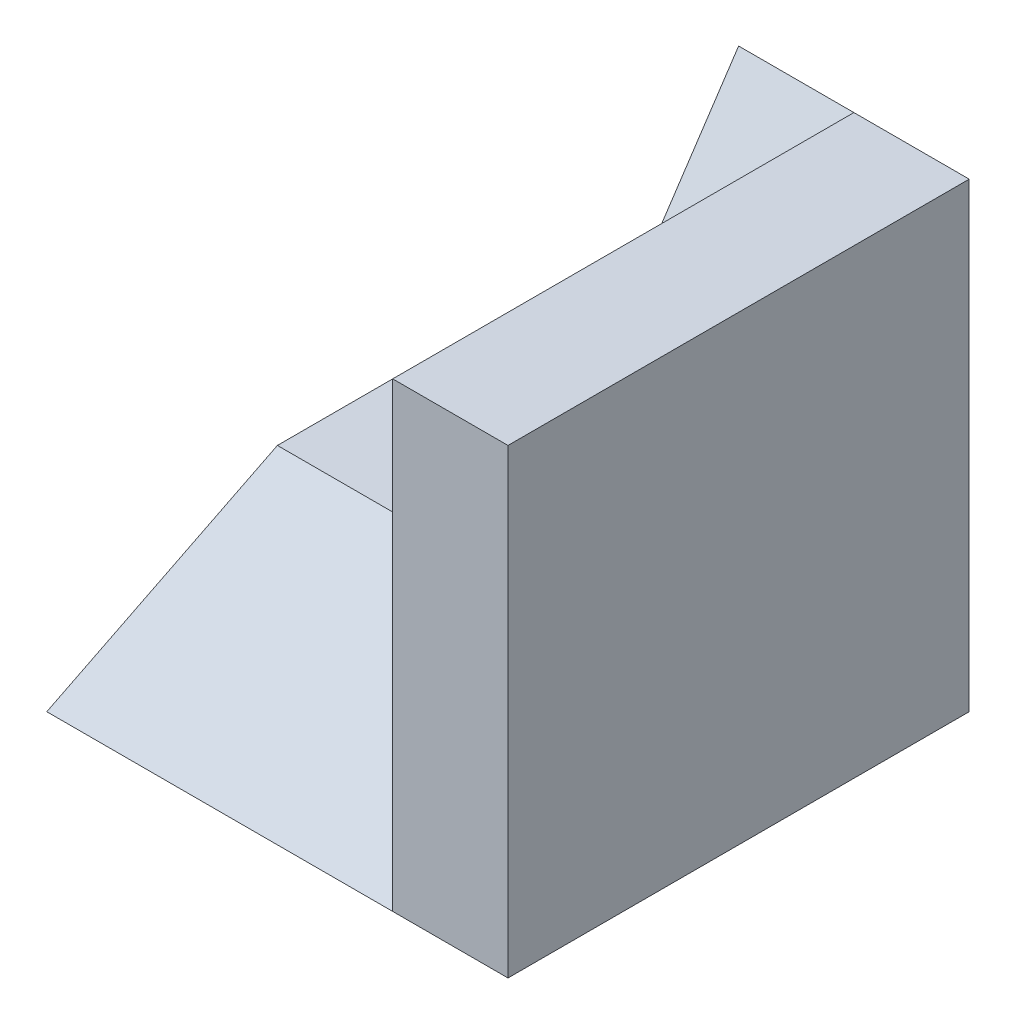
SolidWorks part; units mm, degrees
ref_plane "Front Plane" through (0, 0, 0) normal (0, 0, 1) x (1, 0, 0)
ref_plane "Top Plane" through (0, 0, 0) normal (0, 1, 0) x (1, 0, 0)
ref_plane "Right Plane" through (0, 0, 0) normal (1, 0, 0) x (0, 0, -1)
sketch "Sketch1" plane through (0, 0, 0) normal (0, 1, 0) x (1, 0, 0)
  line L1 (-2, -2) -> (2, -2)
  line L2 (-2, -2) -> (-2, 2)
  line L3 (-2, 2) -> (2, 2)
  line L4 (2, -2) -> (2, 2)
  line L5 (-2, -2) -> (2, 2) construction
  line L6 (-2, 2) -> (2, -2) construction
  point P0 (0, 0)
  dimension "D1" = 4
  dimension "D2" = 4
extrude "Boss-Extrude1" add sketch "Sketch1" along normal blind 4
sketch "Sketch2" plane through (-2, 0, 0) normal (-1, 0, 0) x (0, 0, 1)
  line L0 (-2, 4) -> (0, 1)
  line L1 (0, 1) -> (2, 0)
  line L2 (2, 0) -> (2, 4)
  line L3 (2, 4) -> (-2, 4)
  dimension "D1" = 3
  dimension "D2" = 2
extrude "Cut-Extrude1" cut sketch "Sketch2" against normal blind 3
sketch "Sketch3" plane through (0, 4, 0) normal (0, 1, 0) x (1, 0, 0)
  line L1 (-2, 2) -> (0, 2)
  line L2 (-2, 2) -> (-2, 0)
  line L3 (-2, 0) -> (0, 0)
  line L4 (0, 2) -> (0, 0)
extrude "Cut-Extrude2" cut sketch "Sketch3" against normal blind 3
